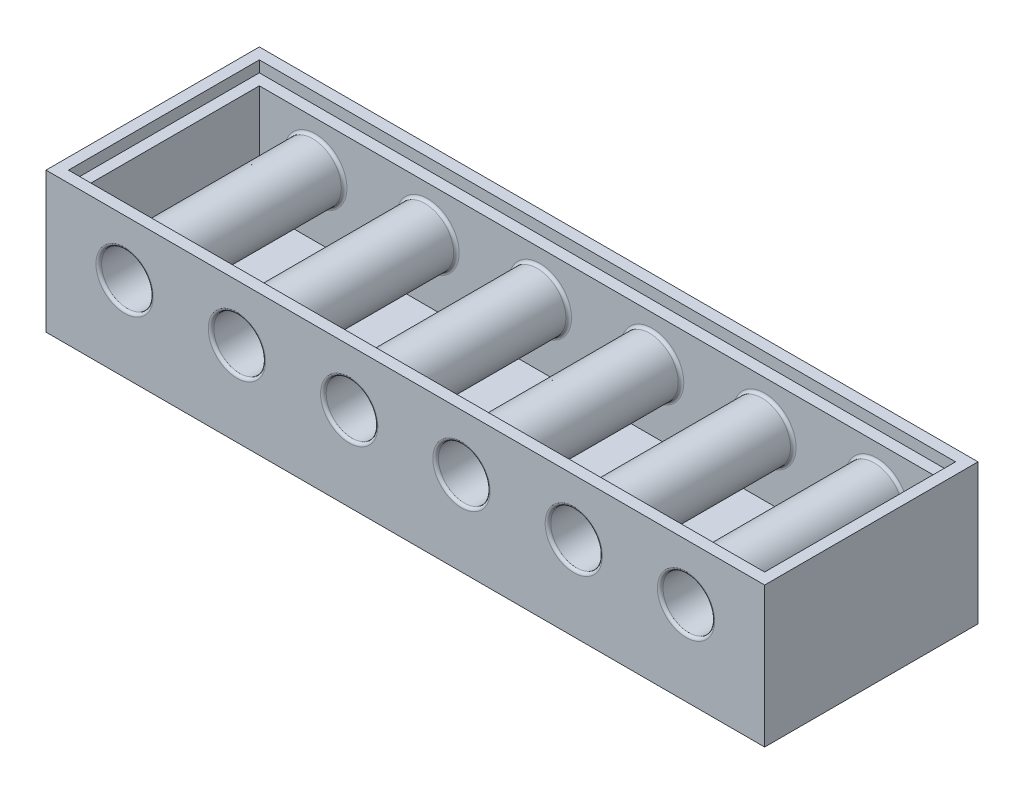
SolidWorks part; units mm, degrees
ref_plane "Front Plane" through (0, 0, 0) normal (0, 0, 1) x (1, 0, 0)
ref_plane "Top Plane" through (0, 0, 0) normal (0, 1, 0) x (1, 0, 0)
ref_plane "Right Plane" through (0, 0, 0) normal (1, 0, 0) x (0, 0, -1)
sketch "Sketch1" plane through (0, 0, 0) normal (0, 1, 0) x (1, 0, 0)
  line L1 (-80, 15) -> (80, 15)
  line L2 (-80, 15) -> (-80, -15)
  line L3 (-80, -15) -> (80, -15)
  line L4 (80, 15) -> (80, -15)
  line L5 (-80, 15) -> (80, -15) construction
  line L6 (-80, -15) -> (80, 15) construction
  point P0 (0, 0)
  dimension "D1" = 30
  dimension "D2" = 160
extrude "Boss-Extrude1" add sketch "Sketch1" along normal blind 4
sketch "Sketch2" plane through (0, 0, 0) normal (0, 1, 0) x (1, 0, 0)
  line L4 (80, -15) -> (80, 15)
  line L5 (80, 15) -> (-80, 15)
  line L6 (-80, 15) -> (-80, -15)
  line L7 (-80, -15) -> (80, -15)
  line L8 (80, -15) -> (80, 15)
  line L9 (80, 15) -> (-80, 15)
  line L10 (-80, 15) -> (-80, -15)
  line L11 (-80, -15) -> (80, -15)
  dimension "D1" = 0
extrude "Extrude-Thin1" add sketch "Sketch2" along normal blind 65 thin
sketch "Sketch4" plane through (0, 0, 19) normal (0, 0, 1) x (1, 0, 0)
  line L0 (-80, 65) -> (-80, 5) construction
  line L1 (-70, 55) -> (-50, 55) construction
  line L2 (-80, 5) -> (80, 5) construction
  line L3 (80, 5) -> (80, 65) construction
  line L4 (-50, 55) -> (-30, 55) construction
  line L5 (80, 65) -> (-80, 65) construction
  line L6 (30, 55) -> (10, 55) construction
  line L7 (80, 65) -> (80, 4) construction
  line L8 (-80, 65) -> (-80, 4) construction
  line L9 (10, 55) -> (-10, 55) construction
  line L10 (-10, 55) -> (-30, 55) construction
  line L11 (30, 55) -> (50, 55) construction
  line L12 (50, 55) -> (70, 55) construction
  line L13 (-84, 65) -> (84, 65) construction
  line L14 (-80, 45) -> (80, 45) construction
  line L15 (-60, 65) -> (-60, 5) construction
  line L16 (-80, 0) -> (80, 0) construction
  circle A0 centre (-70, 55) radius 4.6
  circle A1 centre (-50, 55) radius 4.6
  circle A2 centre (-30, 55) radius 4.6
  circle A3 centre (-10, 55) radius 4.6
  circle A4 centre (10, 55) radius 4.6
  circle A5 centre (30, 55) radius 4.6
  circle A6 centre (50, 55) radius 4.6
  circle A7 centre (70, 55) radius 4.6
  dimension "D10" = 9.2
  dimension "D11" = 9.2
  dimension "D12" = 9.2
  dimension "D13" = 9.2
  dimension "D14" = 9.2
  dimension "D15" = 9.2
  dimension "7" = 9.2
  dimension "D17" = 9.2
  dimension "D2" = 10
  dimension "D3" = 20
  dimension "D4" = 0
  dimension "D5" = 10
  dimension "D6" = 10
  dimension "D7" = 5
  dimension "D8" = 20
extrude "Cut-Extrude1" cut sketch "Sketch4" against normal up to surface (38 mm away) up to face at (0, 32.5, -19)
sketch "Sketch5" plane through (0, 0, 19) normal (0, 0, 1) x (1, 0, 0)
  circle A1 centre (-30, 55) radius 4.6
  circle A2 centre (-30, 55) radius 4.6
  circle A3 centre (-50, 55) radius 4.6
  circle A4 centre (-50, 55) radius 4.6
  circle A5 centre (70, 55) radius 4.6
  circle A6 centre (70, 55) radius 4.6
  circle A7 centre (50, 55) radius 4.6
  circle A8 centre (50, 55) radius 4.6
  circle A9 centre (30, 55) radius 4.6
  circle A10 centre (30, 55) radius 4.6
  circle A11 centre (10, 55) radius 4.6
  circle A12 centre (10, 55) radius 4.6
  circle A13 centre (-10, 55) radius 4.6
  circle A14 centre (-10, 55) radius 4.6
  circle A15 centre (-70, 55) radius 4.6
  circle A16 centre (-70, 55) radius 4.6
  dimension "D1" = 0
  dimension "D2" = 0
  dimension "D3" = 0
  dimension "D4" = 0
  dimension "D5" = 0
  dimension "D6" = 0
  dimension "D7" = 0
  dimension "D8" = 0
extrude "Extrude-Thin3" add sketch "Sketch5" against normal up to surface (38 mm away) thin
pattern_linear "LPattern1" count 3 spacing 20 along (0, -1, 0) of "Cut-Extrude1", "Extrude-Thin3"
sketch "Sketch7" plane through (0, 0, 19) normal (0, 0, 1) x (1, 0, 0)
  line L0 (44, 65) -> (44, 0)
  line L1 (-84, 65) -> (84, 65) construction
  line L2 (-80, 0) -> (80, 0) construction
  line L3 (44, 0) -> (40, 0)
  line L4 (40, 0) -> (40, 65)
  line L5 (40, 65) -> (44, 65)
  circle A2 centre (30, 55) radius 4.6 construction
  dimension "D1" = 10
  dimension "D2" = 4
extrude "Boss-Extrude2" add sketch "Sketch7" against normal through all
sketch "Sketch9" plane through (0, 0, 19) normal (0, 0, 1) x (1, 0, 0)
  line L0 (44, 65) -> (44, 0)
  line L1 (-84, 65) -> (84, 65) construction
  line L2 (-80, 0) -> (80, 0) construction
  circle A0 centre (30, 55) radius 4.6 construction
  dimension "D1" = 14
extrude "Cut-Extrude2" cut sketch "Sketch9" along normal through all and the other way through all
sketch "Sketch10" plane through (0, 0, 19) normal (0, 0, 1) x (1, 0, 0)
  line L0 (-70, 35) -> (-70, 15) construction
  line L1 (-84, 25) -> (44, 25)
  line L3 (-84, 65) -> (-84, 0) construction
  line L4 (44, 0) -> (44, 65) construction
  point P10 (-70, 25)
extrude "Cut-Extrude3" cut sketch "Sketch10" against normal through all and the other way through all
sketch "Sketch11" plane through (0, 25, 0) normal (0, 1, 0) x (1, 0, 0)
  line L0 (-80, 15) -> (-84, 15) construction
  line L1 (-82, 17) -> (42, 17)
  line L2 (-82, 17) -> (-82, -17)
  line L3 (-82, -17) -> (42, -17)
  line L4 (42, 17) -> (42, -17)
  line L5 (-84, -19) -> (-84, 19) construction
  line L6 (-80, 15) -> (-80, 19) construction
  line L7 (44, 19) -> (-84, 19) construction
  line L8 (40, -15) -> (44, -15) construction
  line L9 (-80, -15) -> (80, -15) construction
  line L10 (44, -19) -> (44, 19) construction
  line L11 (40, -15) -> (40, -19) construction
  line L12 (-84, -19) -> (44, -19) construction
  point P19 (-80, 17)
  point P23 (-82, 15)
  point P24 (40, -17)
  point P25 (42, -15)
extrude "Cut-Extrude4" cut sketch "Sketch11" against normal blind 2
fillet "Fillet1" radius 0.5 24 edges at (34.6, 15, -19) (34.6, 15, 19) (14.6, 15, -19) (14.6, 15, 19) (-5.4, 15, -19) (-5.4, 15, 19) (-65.4, 15, -19) (-65.4, 15, 19) (-25.4, 15, -19) (-25.4, 15, 19) (-45.4, 15, -19) (-45.4, 15, 19) (-24.9, 15, -15) (-35.1, 15, 15) (-44.9, 15, -15) (-55.1, 15, 15) (35.1, 15, -15) (24.9, 15, 15) (15.1, 15, -15) (4.9, 15, 15) (-4.9, 15, -15) (-15.1, 15, 15) (-64.9, 15, -15) (-75.1, 15, 15)
equation "\"59、\"=60.575"
